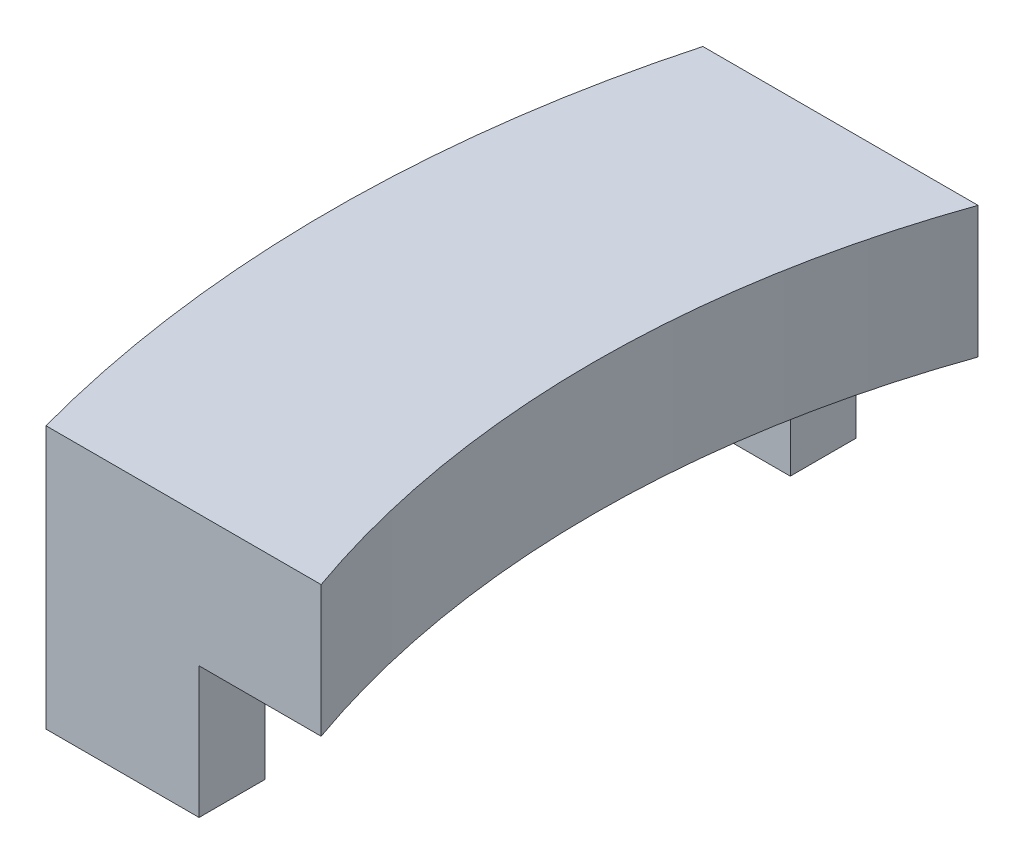
SolidWorks part; units mm, degrees
ref_plane "Front Plane" through (0, 0, 0) normal (0, 0, 1) x (1, 0, 0)
ref_plane "Top Plane" through (0, 0, 0) normal (0, 1, 0) x (1, 0, 0)
ref_plane "Right Plane" through (0, 0, 0) normal (1, 0, 0) x (0, 0, -1)
sketch "Sketch1" plane through (0, 0, 0) normal (0, 1, 0) x (1, 0, 0)
  line L0 (-18.3303, 5) -> (-14.1421, 5)
  line L1 (-18.3303, -5) -> (-14.1421, -5)
  line L2 (0, 0) -> (-15, 0) construction
  arc A0 (-18.3303, 5) -> (-18.3303, -5) centre (0, 0) ccw
  arc A1 (-14.1421, 5) -> (-14.1421, -5) centre (0, 0) ccw
  dimension "D1" = 30
  dimension "D2" = 38
  dimension "D3" = 5
  dimension "D4" = 5
extrude "Boss-Extrude1" add sketch "Sketch1" along normal blind 2
sketch "Sketch2" plane through (0, 0, 0) normal (0, -1, 0) x (1, 0, 0)
  line L0 (-14.1421, -5) -> (-18.3303, -5) construction
  line L1 (-18.3303, 5) -> (-14.1421, 5) construction
  line L2 (-16, -5) -> (-18.3303, -5)
  line L3 (-18.3303, 5) -> (-16, 5)
  line L4 (-18.5742, 4) -> (-16, 4)
  line L5 (-18.5742, -4) -> (-16, -4)
  line L6 (-16, 5) -> (-16, 4)
  line L7 (-16, -4) -> (-16, -5)
  arc A0 (-18.3303, 5) -> (-18.3303, -5) centre (0, 0) ccw construction
  arc A1 (-14.1421, 5) -> (-14.1421, -5) centre (0, 0) ccw construction
  arc A2 (-18.3303, 5) -> (-18.5742, 4) centre (0, 0) ccw
  arc A4 (-18.5742, -4) -> (-18.3303, -5) centre (0, 0) ccw
  dimension "D1" = 1
  dimension "D2" = 1
  dimension "D3" = 16
extrude "Boss-Extrude2" add sketch "Sketch2" along normal blind 2
